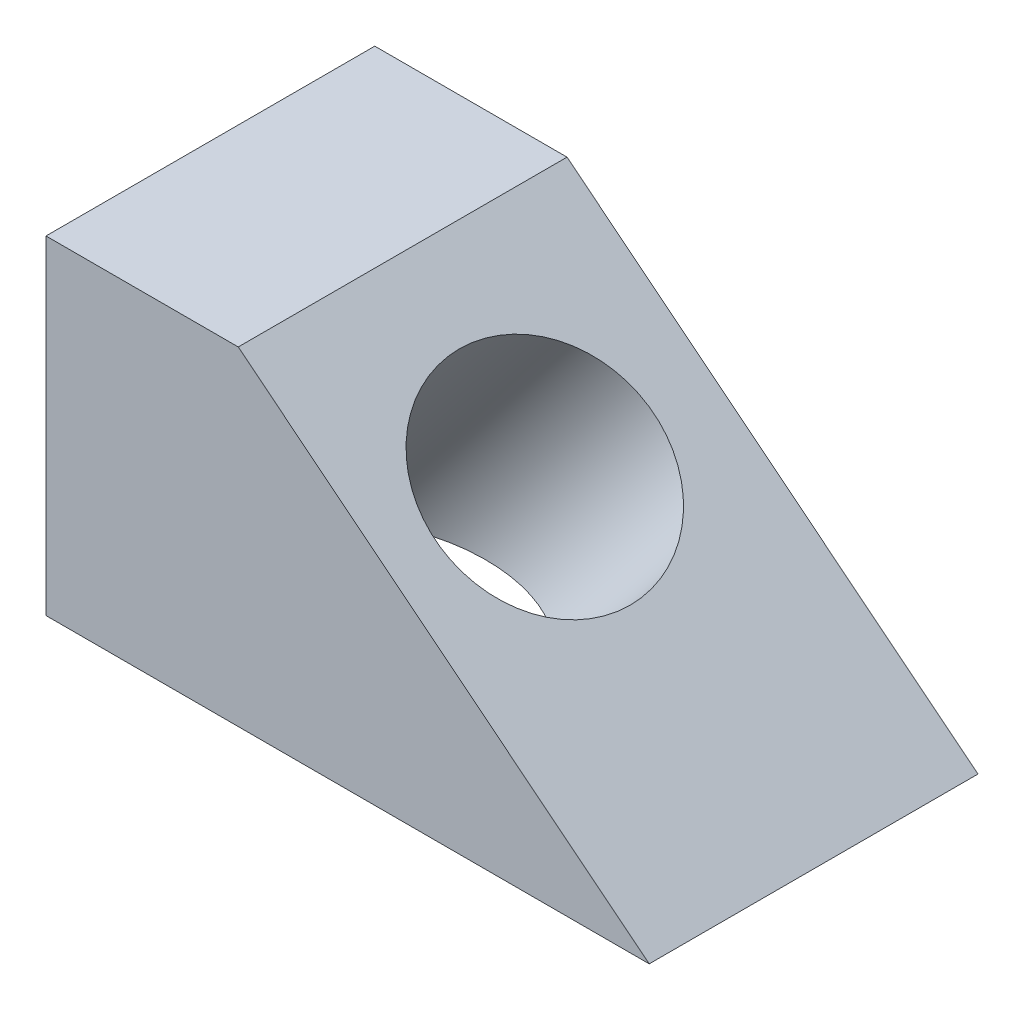
SolidWorks part; units mm, degrees
ref_plane "Front Plane" through (0, 0, 0) normal (0, 0, 1) x (1, 0, 0)
ref_plane "Top Plane" through (0, 0, 0) normal (0, 1, 0) x (1, 0, 0)
ref_plane "Right Plane" through (0, 0, 0) normal (1, 0, 0) x (0, 0, -1)
sketch "Sketch1" plane through (0, 0, 0) normal (0, 0, 1) x (1, 0, 0)
  line L0 (0, 0) -> (0, 59.944)
  line L1 (0, 59.944) -> (35.052, 59.944)
  line L2 (35.052, 59.944) -> (109.982, 0)
  line L3 (109.982, 0) -> (0, 0)
  dimension "D1" = 59.944
  dimension "D2" = 35.052
  dimension "D3" = 109.982
extrude "Boss-Extrude1" add sketch "Sketch1" along normal mid plane 59.944 contours L2 L3 L0 L1
sketch "Sketch2" plane through (42.9198, 53.6498, 0) normal (0.6247, 0.7809, 0) x (0.7809, -0.6247, 0)
  line L0 (-10.0757, -29.972) -> (85.8815, -29.972) construction
  line L1 (85.8815, -29.972) -> (85.8815, 29.972) construction
  circle A0 centre (24.4135, -1.016) radius 19.939
  dimension "D1" = 39.878
  dimension "D3" = 61.468
  dimension "D2" = 28.956
extrude "Cut-Extrude1" cut sketch "Sketch2" against normal up to surface (65.1256 mm away)
